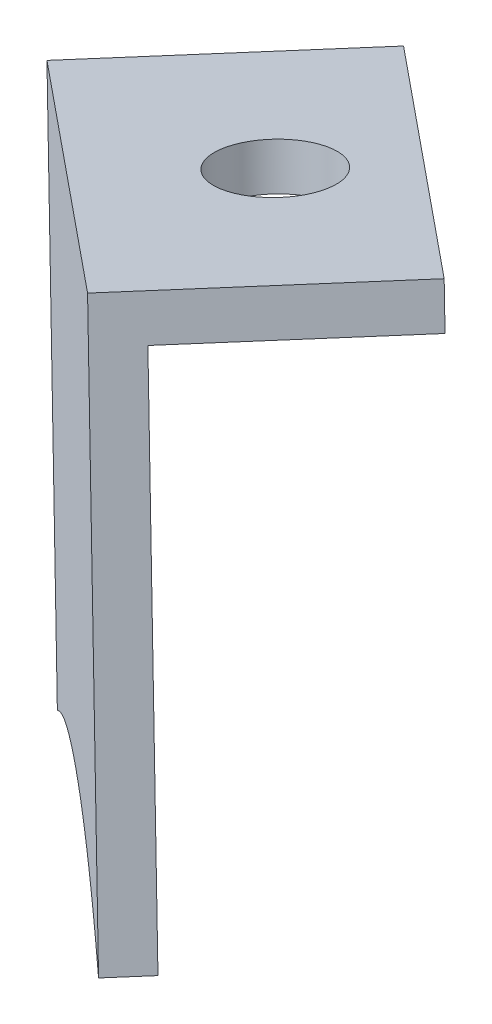
SolidWorks part; units mm, degrees
material "1.4105 (X6CrMoS17)"
ref_plane "Płaszczyzna XY" through (0, 0, 0) normal (0, 0, 1) x (1, 0, 0)
ref_plane "Płaszczyzna XZ" through (0, 0, 0) normal (0, 1, 0) x (1, 0, 0)
ref_plane "Płaszczyzna YZ" through (0, 0, 0) normal (1, 0, 0) x (0, 0, -1)
ref_plane "Płaszczyzna2" through (184.0502, 0, -211.7255) normal (0.6561, 0, -0.7547) x (-0.7547, 0, -0.6561)
sketch "Szkic1" plane through (184.0502, 0, -211.7255) normal (0.6561, 0, -0.7547) x (-0.7547, 0, -0.6561)
  line L2 (-985.6973, -340.2595) -> (-980.4192, -315.8231)
  line L3 (-965.8795, -343.2386) -> (-960.87, -320.0455)
  line L4 (-980.4192, -315.8231) -> (-960.87, -320.0455)
  spline S0 degree 3 poles (-990.9279, -345.3576) (-980.8954, -322.4589) (-949.3258, -336.2904) (-959.3583, -359.189) (-969.3908, -382.0877) (-1000.9604, -368.2563) (-990.9279, -345.3576) (-980.8954, -322.4589) (-949.3258, -336.2904) knots -0.5 0 0 0 0.5 0.5 0.5 1 1 1 1.5 1.5 1.5 weights 1 0.333333 0.333333 1 0.333333 0.333333 1 0.333333 0.333333 only from (-990.9279, -345.3576) to (-990.9279, -345.3576)
  spline S1 degree 3 poles (-985.6973, -340.2595) (-980.094, -337.678) (-972.489, -338.4904) (-965.8795, -343.2386) knots 0.113653 0.113653 0.113653 0.113653 0.285977 0.285977 0.285977 0.285977 weights 0.648724 0.523413 0.47729 0.510355
  dimension "D1" = 90
  dimension "D2" = 23.7279
  dimension "D4" = 20
  dimension "D6" = 25
  dimension "D9" = 980.4192
extrude "Dodanie-wyciągnięcie1" add sketch "Szkic1" along normal blind 2
ref_plane "Płaszczyzna3" through (185.3623, 0, -213.2349) normal (0.6561, 0, -0.7547) x (-0.7547, 0, -0.6561)
sketch "Szkic2" plane through (185.3623, 0, -213.2349) normal (0.6561, 0, -0.7547) x (-0.7547, 0, -0.6561)
  line L0 (-980.4192, -315.8231) -> (-960.87, -320.0455)
extrude "Wyciągnięcie-cienka ścianka1" add sketch "Szkic2" along normal blind 10 thin
ref_plane "Płaszczyzna4" through (82.4875, -506.0243, 71.7053) normal (0.1593, -0.9775, 0.1385) x (-0.9872, -0.1578, 0.0224)
sketch "Szkic3" plane through (82.4875, -506.0243, 71.7053) normal (0.1593, -0.9775, 0.1385) x (-0.9872, -0.1578, 0.0224)
  line L0 (-860.6816, -373.942) -> (-845.7367, -360.651) construction
  line L1 (-860.6816, -373.942) -> (-854.0361, -381.4144) construction
  circle A0 centre (-849.8864, -371.0327) radius 2.5
  dimension "D1" = 5
  dimension "D2" = 5
  dimension "D3" = 10
extrude "Wytnij-wyciągnięcie1" cut sketch "Szkic3" against normal blind 10
